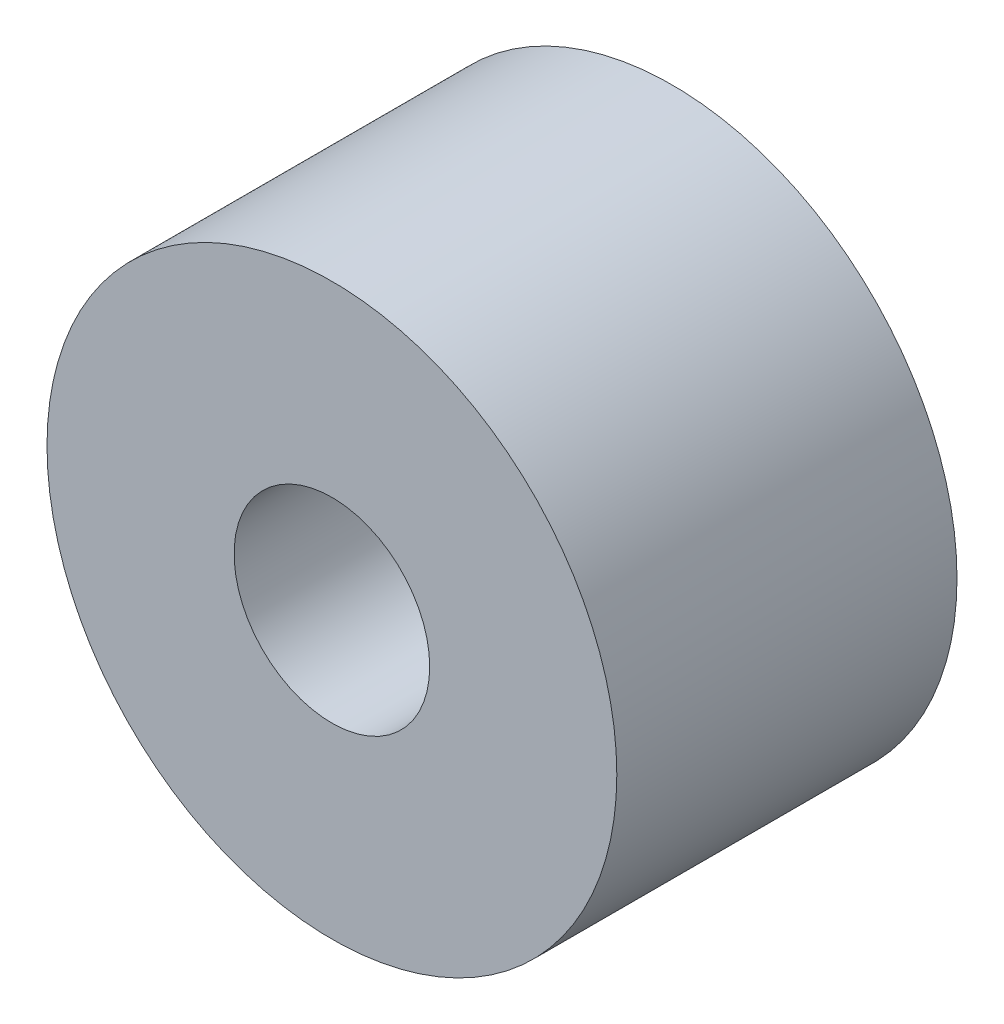
SolidWorks part; units mm, degrees
ref_plane "Front Plane" through (0, 0, 0) normal (0, 0, 1) x (1, 0, 0)
ref_plane "Top Plane" through (0, 0, 0) normal (0, 1, 0) x (1, 0, 0)
ref_plane "Right Plane" through (0, 0, 0) normal (1, 0, 0) x (0, 0, -1)
sketch "Sketch1" plane through (0, 0, 0) normal (0, 0, 1) x (1, 0, 0)
  circle A0 centre (0, 0) radius 4.2545
  circle A1 centre (0, 0) radius 1.4605
  dimension "D1" = 8.509
  dimension "D2" = 2.921
extrude "Boss-Extrude1" add sketch "Sketch1" along normal blind 5.08
